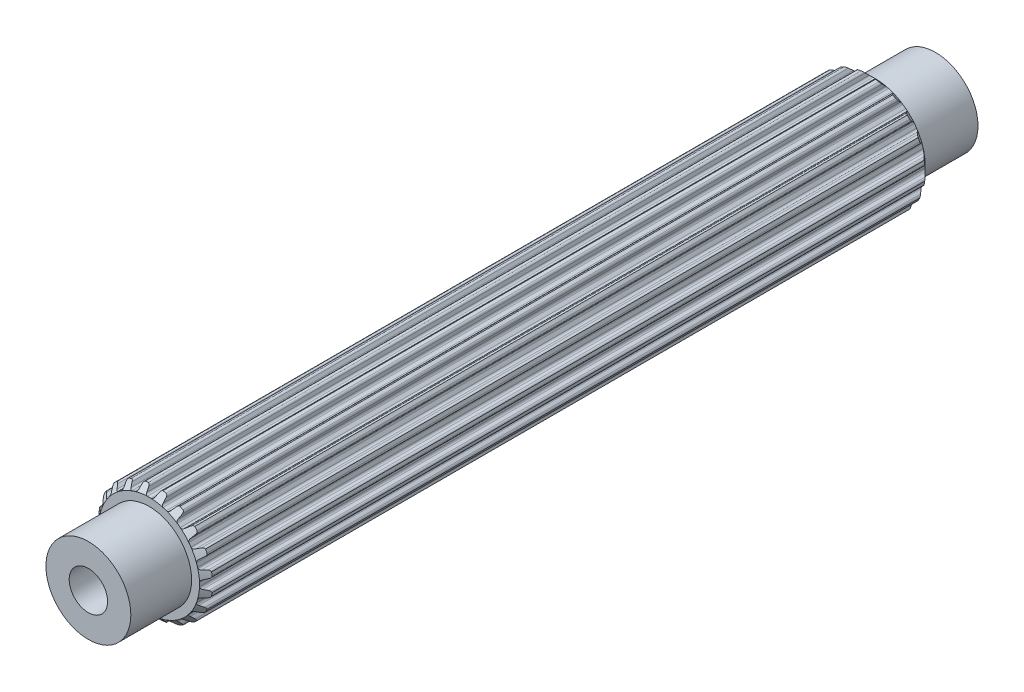
SolidWorks part; units mm, degrees
ref_plane "Front Plane" through (0, 0, 0) normal (0, 0, 1) x (1, 0, 0)
ref_plane "Top Plane" through (0, 0, 0) normal (0, 1, 0) x (1, 0, 0)
ref_plane "Right Plane" through (0, 0, 0) normal (1, 0, 0) x (0, 0, -1)
sketch "Sketch1" plane through (0, 0, 0) normal (0, 0, 1) x (1, 0, 0)
  line L0 (-0.1069, 2.9699) -> (0.1069, 2.9699)
  line L1 (0.3159, 3.2375) -> (0.2537, 3.0575)
  line L2 (-0.2964, 3.2367) -> (-0.2318, 3.0575)
  line L3 (-0.2964, 3.2367) -> (0.3159, 3.2375) construction
  line L4 (0, 3.3252) -> (0, 0) construction
  line L5 (-0.2318, 3.0575) -> (0.2537, 3.0575) construction
  line L6 (-0.4281, 3.3241) -> (0.4281, 3.3263) construction
  line L7 (0.7183, 3.1698) -> (0.7244, 2.9795)
  line L8 (0.816, 2.8576) -> (1.0195, 2.7915)
  line L9 (1.3009, 2.9815) -> (1.1862, 2.8295)
  line L10 (1.6627, 2.7927) -> (1.6097, 2.6099)
  line L11 (1.6591, 2.4655) -> (1.8322, 2.3398)
  line L12 (2.1585, 2.4335) -> (2.0025, 2.3245)
  line L13 (2.4443, 2.1423) -> (2.3374, 1.9847)
  line L14 (2.3398, 1.8322) -> (2.4655, 1.6591)
  line L15 (2.8049, 1.6474) -> (2.6228, 1.5919)
  line L16 (2.9866, 1.2821) -> (2.8363, 1.1653)
  line L17 (2.7915, 1.0195) -> (2.8576, 0.816)
  line L18 (3.1767, 0.7) -> (2.9863, 0.7035)
  line L19 (3.2367, 0.2964) -> (3.0575, 0.2318)
  line L20 (2.9699, 0.1069) -> (2.9699, -0.1069)
  line L21 (3.2375, -0.3159) -> (3.0575, -0.2537)
  line L22 (3.1698, -0.7183) -> (2.9795, -0.7244)
  line L23 (2.8576, -0.816) -> (2.7915, -1.0195)
  line L24 (2.9815, -1.3009) -> (2.8295, -1.1862)
  line L25 (2.7927, -1.6627) -> (2.6099, -1.6097)
  line L26 (2.4655, -1.6591) -> (2.3398, -1.8322)
  line L27 (2.4335, -2.1585) -> (2.3245, -2.0025)
  line L28 (2.1423, -2.4443) -> (1.9847, -2.3374)
  line L29 (1.8322, -2.3398) -> (1.6591, -2.4655)
  line L30 (1.6474, -2.8049) -> (1.5919, -2.6228)
  line L31 (1.2821, -2.9866) -> (1.1653, -2.8363)
  line L32 (1.0195, -2.7915) -> (0.816, -2.8576)
  line L33 (0.7, -3.1767) -> (0.7035, -2.9863)
  line L34 (0.2964, -3.2367) -> (0.2318, -3.0575)
  line L35 (0.1069, -2.9699) -> (-0.1069, -2.9699)
  line L36 (-0.3159, -3.2375) -> (-0.2537, -3.0575)
  line L37 (-0.7183, -3.1698) -> (-0.7244, -2.9795)
  line L38 (-0.816, -2.8576) -> (-1.0195, -2.7915)
  line L39 (-1.3009, -2.9815) -> (-1.1862, -2.8295)
  line L40 (-1.6627, -2.7927) -> (-1.6097, -2.6099)
  line L41 (-1.6591, -2.4655) -> (-1.8322, -2.3398)
  line L42 (-2.1585, -2.4335) -> (-2.0025, -2.3245)
  line L43 (-2.4443, -2.1423) -> (-2.3374, -1.9847)
  line L44 (-2.3398, -1.8322) -> (-2.4655, -1.6591)
  line L45 (-2.8049, -1.6474) -> (-2.6228, -1.5919)
  line L46 (-2.9866, -1.2821) -> (-2.8363, -1.1653)
  line L47 (-2.7915, -1.0195) -> (-2.8576, -0.816)
  line L48 (-3.1767, -0.7) -> (-2.9863, -0.7035)
  line L49 (-3.2367, -0.2964) -> (-3.0575, -0.2318)
  line L50 (-2.9699, -0.1069) -> (-2.9699, 0.1069)
  line L51 (-3.2375, 0.3159) -> (-3.0575, 0.2537)
  line L52 (-3.1698, 0.7183) -> (-2.9795, 0.7244)
  line L53 (-2.8576, 0.816) -> (-2.7915, 1.0195)
  line L54 (-2.9815, 1.3009) -> (-2.8295, 1.1862)
  line L55 (-2.7927, 1.6627) -> (-2.6099, 1.6097)
  line L56 (-2.4655, 1.6591) -> (-2.3398, 1.8322)
  line L57 (-2.4335, 2.1585) -> (-2.3245, 2.0025)
  line L58 (-2.1423, 2.4443) -> (-1.9847, 2.3374)
  line L59 (-1.8322, 2.3398) -> (-1.6591, 2.4655)
  line L60 (-1.6474, 2.8049) -> (-1.5919, 2.6228)
  line L61 (-1.2821, 2.9866) -> (-1.1653, 2.8363)
  line L62 (-1.0195, 2.7915) -> (-0.816, 2.8576)
  line L63 (-0.7, 3.1767) -> (-0.7035, 2.9863)
  line L64 (0.4281, 3.3263) -> (0.62, 3.2938)
  line L65 (1.4351, 3.0312) -> (1.6075, 2.9409)
  line L66 (2.3015, 2.4394) -> (2.4376, 2.3003)
  line L67 (2.9427, 1.6088) -> (3.0291, 1.4344)
  line L68 (3.2958, 0.6207) -> (3.3241, 0.4281)
  line L69 (3.3263, -0.4281) -> (3.2938, -0.62)
  line L70 (3.0312, -1.4351) -> (2.9409, -1.6075)
  line L71 (2.4394, -2.3015) -> (2.3003, -2.4376)
  line L72 (1.6088, -2.9427) -> (1.4344, -3.0291)
  line L73 (0.6207, -3.2958) -> (0.4281, -3.3241)
  line L74 (-0.4281, -3.3263) -> (-0.62, -3.2938)
  line L75 (-1.4351, -3.0312) -> (-1.6075, -2.9409)
  line L76 (-2.3015, -2.4394) -> (-2.4376, -2.3003)
  line L77 (-2.9427, -1.6088) -> (-3.0291, -1.4344)
  line L78 (-3.2958, -0.6207) -> (-3.3241, -0.4281)
  line L79 (-3.3263, 0.4281) -> (-3.2938, 0.62)
  line L80 (-3.0312, 1.4351) -> (-2.9409, 1.6075)
  line L81 (-2.4394, 2.3015) -> (-2.3003, 2.4376)
  line L82 (-1.6088, 2.9427) -> (-1.4344, 3.0291)
  line L83 (-0.6207, 3.2958) -> (-0.4281, 3.3241)
  arc A0 (0.2537, 3.0575) -> (0.1069, 2.9699) centre (0.1283, 3.1009) cw
  arc A1 (-0.2318, 3.0575) -> (-0.1069, 2.9699) centre (-0.1069, 3.1026) ccw
  arc A2 (0.62, 3.2938) -> (0.7183, 3.1698) centre (0.5856, 3.1656) cw
  arc A3 (0.7244, 2.9795) -> (0.816, 2.8576) centre (0.857, 2.9838) ccw
  arc A4 (-0.4281, 3.3241) -> (-0.2964, 3.2367) centre (-0.4213, 3.1916) cw
  arc A5 (0.4281, 3.3263) -> (0.3159, 3.2375) centre (0.4413, 3.1942) ccw
  arc A6 (1.1862, 2.8295) -> (1.0195, 2.7915) centre (1.0802, 2.9095) cw
  arc A7 (1.4351, 3.0312) -> (1.3009, 2.9815) centre (1.4068, 2.9015) ccw
  arc A8 (1.6075, 2.9409) -> (1.6627, 2.7927) centre (1.5352, 2.8297) cw
  arc A9 (1.6097, 2.6099) -> (1.6591, 2.4655) centre (1.7371, 2.5729) ccw
  arc A10 (2.0025, 2.3245) -> (1.8322, 2.3398) centre (1.9264, 2.4332) cw
  arc A11 (2.3015, 2.4394) -> (2.1585, 2.4335) centre (2.2346, 2.3248) ccw
  arc A12 (2.4376, 2.3003) -> (2.4443, 2.1423) centre (2.3345, 2.2168) cw
  arc A13 (2.3374, 1.9847) -> (2.3398, 1.8322) centre (2.4472, 1.9102) ccw
  arc A14 (2.6228, 1.5919) -> (2.4655, 1.6591) centre (2.5841, 1.7189) cw
  arc A15 (2.9427, 1.6088) -> (2.8049, 1.6474) centre (2.8436, 1.5205) ccw
  arc A16 (3.0291, 1.4344) -> (2.9866, 1.2821) centre (2.9052, 1.3869) cw
  arc A17 (2.8363, 1.1653) -> (2.7915, 1.0195) centre (2.9177, 1.0605) ccw
  arc A18 (2.9863, 0.7035) -> (2.8576, 0.816) centre (2.9887, 0.8362) cw
  arc A19 (3.2958, 0.6207) -> (3.1767, 0.7) centre (3.1743, 0.5673) ccw
  arc A20 (3.3241, 0.4281) -> (3.2367, 0.2964) centre (3.1916, 0.4213) cw
  arc A21 (3.0575, 0.2318) -> (2.9699, 0.1069) centre (3.1026, 0.1069) ccw
  arc A22 (3.0575, -0.2537) -> (2.9699, -0.1069) centre (3.1009, -0.1283) cw
  arc A23 (3.3263, -0.4281) -> (3.2375, -0.3159) centre (3.1942, -0.4413) ccw
  arc A24 (3.2938, -0.62) -> (3.1698, -0.7183) centre (3.1656, -0.5856) cw
  arc A25 (2.9795, -0.7244) -> (2.8576, -0.816) centre (2.9838, -0.857) ccw
  arc A26 (2.8295, -1.1862) -> (2.7915, -1.0195) centre (2.9095, -1.0802) cw
  arc A27 (3.0312, -1.4351) -> (2.9815, -1.3009) centre (2.9015, -1.4068) ccw
  arc A28 (2.9409, -1.6075) -> (2.7927, -1.6627) centre (2.8297, -1.5352) cw
  arc A29 (2.6099, -1.6097) -> (2.4655, -1.6591) centre (2.5729, -1.7371) ccw
  arc A30 (2.3245, -2.0025) -> (2.3398, -1.8322) centre (2.4332, -1.9264) cw
  arc A31 (2.4394, -2.3015) -> (2.4335, -2.1585) centre (2.3248, -2.2346) ccw
  arc A32 (2.3003, -2.4376) -> (2.1423, -2.4443) centre (2.2168, -2.3345) cw
  arc A33 (1.9847, -2.3374) -> (1.8322, -2.3398) centre (1.9102, -2.4472) ccw
  arc A34 (1.5919, -2.6228) -> (1.6591, -2.4655) centre (1.7189, -2.5841) cw
  arc A35 (1.6088, -2.9427) -> (1.6474, -2.8049) centre (1.5205, -2.8436) ccw
  arc A36 (1.4344, -3.0291) -> (1.2821, -2.9866) centre (1.3869, -2.9052) cw
  arc A37 (1.1653, -2.8363) -> (1.0195, -2.7915) centre (1.0605, -2.9177) ccw
  arc A38 (0.7035, -2.9863) -> (0.816, -2.8576) centre (0.8362, -2.9887) cw
  arc A39 (0.6207, -3.2958) -> (0.7, -3.1767) centre (0.5673, -3.1743) ccw
  arc A40 (0.4281, -3.3241) -> (0.2964, -3.2367) centre (0.4213, -3.1916) cw
  arc A41 (0.2318, -3.0575) -> (0.1069, -2.9699) centre (0.1069, -3.1026) ccw
  arc A42 (-0.2537, -3.0575) -> (-0.1069, -2.9699) centre (-0.1283, -3.1009) cw
  arc A43 (-0.4281, -3.3263) -> (-0.3159, -3.2375) centre (-0.4413, -3.1942) ccw
  arc A44 (-0.62, -3.2938) -> (-0.7183, -3.1698) centre (-0.5856, -3.1656) cw
  arc A45 (-0.7244, -2.9795) -> (-0.816, -2.8576) centre (-0.857, -2.9838) ccw
  arc A46 (-1.1862, -2.8295) -> (-1.0195, -2.7915) centre (-1.0802, -2.9095) cw
  arc A47 (-1.4351, -3.0312) -> (-1.3009, -2.9815) centre (-1.4068, -2.9015) ccw
  arc A48 (-1.6075, -2.9409) -> (-1.6627, -2.7927) centre (-1.5352, -2.8297) cw
  arc A49 (-1.6097, -2.6099) -> (-1.6591, -2.4655) centre (-1.7371, -2.5729) ccw
  arc A50 (-2.0025, -2.3245) -> (-1.8322, -2.3398) centre (-1.9264, -2.4332) cw
  arc A51 (-2.3015, -2.4394) -> (-2.1585, -2.4335) centre (-2.2346, -2.3248) ccw
  arc A52 (-2.4376, -2.3003) -> (-2.4443, -2.1423) centre (-2.3345, -2.2168) cw
  arc A53 (-2.3374, -1.9847) -> (-2.3398, -1.8322) centre (-2.4472, -1.9102) ccw
  arc A54 (-2.6228, -1.5919) -> (-2.4655, -1.6591) centre (-2.5841, -1.7189) cw
  arc A55 (-2.9427, -1.6088) -> (-2.8049, -1.6474) centre (-2.8436, -1.5205) ccw
  arc A56 (-3.0291, -1.4344) -> (-2.9866, -1.2821) centre (-2.9052, -1.3869) cw
  arc A57 (-2.8363, -1.1653) -> (-2.7915, -1.0195) centre (-2.9177, -1.0605) ccw
  arc A58 (-2.9863, -0.7035) -> (-2.8576, -0.816) centre (-2.9887, -0.8362) cw
  arc A59 (-3.2958, -0.6207) -> (-3.1767, -0.7) centre (-3.1743, -0.5673) ccw
  arc A60 (-3.3241, -0.4281) -> (-3.2367, -0.2964) centre (-3.1916, -0.4213) cw
  arc A61 (-3.0575, -0.2318) -> (-2.9699, -0.1069) centre (-3.1026, -0.1069) ccw
  arc A62 (-3.0575, 0.2537) -> (-2.9699, 0.1069) centre (-3.1009, 0.1283) cw
  arc A63 (-3.3263, 0.4281) -> (-3.2375, 0.3159) centre (-3.1942, 0.4413) ccw
  arc A64 (-3.2938, 0.62) -> (-3.1698, 0.7183) centre (-3.1656, 0.5856) cw
  arc A65 (-2.9795, 0.7244) -> (-2.8576, 0.816) centre (-2.9838, 0.857) ccw
  arc A66 (-2.8295, 1.1862) -> (-2.7915, 1.0195) centre (-2.9095, 1.0802) cw
  arc A67 (-3.0312, 1.4351) -> (-2.9815, 1.3009) centre (-2.9015, 1.4068) ccw
  arc A68 (-2.9409, 1.6075) -> (-2.7927, 1.6627) centre (-2.8297, 1.5352) cw
  arc A69 (-2.6099, 1.6097) -> (-2.4655, 1.6591) centre (-2.5729, 1.7371) ccw
  arc A70 (-2.3245, 2.0025) -> (-2.3398, 1.8322) centre (-2.4332, 1.9264) cw
  arc A71 (-2.4394, 2.3015) -> (-2.4335, 2.1585) centre (-2.3248, 2.2346) ccw
  arc A72 (-2.3003, 2.4376) -> (-2.1423, 2.4443) centre (-2.2168, 2.3345) cw
  arc A73 (-1.9847, 2.3374) -> (-1.8322, 2.3398) centre (-1.9102, 2.4472) ccw
  arc A74 (-1.5919, 2.6228) -> (-1.6591, 2.4655) centre (-1.7189, 2.5841) cw
  arc A75 (-1.6088, 2.9427) -> (-1.6474, 2.8049) centre (-1.5205, 2.8436) ccw
  arc A76 (-1.4344, 3.0291) -> (-1.2821, 2.9866) centre (-1.3869, 2.9052) cw
  arc A77 (-1.1653, 2.8363) -> (-1.0195, 2.7915) centre (-1.0605, 2.9177) ccw
  arc A78 (-0.7035, 2.9863) -> (-0.816, 2.8576) centre (-0.8362, 2.9887) cw
  arc A79 (-0.6207, 3.2958) -> (-0.7, 3.1767) centre (-0.5673, 3.1743) ccw
  point P14 (0, 2.9699)
  point P247 (0, 0)
  dimension "D4" = 0.1327
  dimension "D8" = 20
  dimension "D1" = 2.9699
  dimension "D2" = 0.2139
  dimension "D3" = 0.1904
  dimension "D5" = 0.0877
  dimension "D6" = 0.4855
  dimension "D7" = 0.8563
extrude "Boss-Extrude1" add sketch "Sketch1" along normal mid plane 42.7584
sketch "Sketch2" plane through (0, 0, 0) normal (0, 0, 1) x (1, 0, 0)
  circle A0 centre (0, 0) radius 2.5019
  dimension "D1" = 5.0038
extrude "Boss-Extrude2" add sketch "Sketch2" along normal mid plane 49.9212
sketch "Sketch4" plane through (0, 0, 24.9606) normal (0, 0, 1) x (1, 0, 0)
  circle A0 centre (0, 0) radius 2.5019 construction
  point P0 (0, 0)
sketch "Sketch5" plane through (0, 0, -24.9606) normal (0, 0, -1) x (-1, 0, 0)
  circle A0 centre (0, 0) radius 2.5019 construction
  point P0 (0, 0)
sketch "Sketch3" plane through (0, 0, 0) normal (1, 0, 0) x (0, 0, -1)
  line L0 (-20.248, 4.1011) -> (-21.3792, 2.9699)
  line L1 (-21.3792, 2.9699) -> (-21.3792, 4.1011)
  line L2 (-21.3792, 4.1011) -> (-20.248, 4.1011)
  line L3 (-21.3792, 2.5019) -> (-21.3792, -2.5019) construction
  line L5 (-14.3608, 0) -> (13.2171, 0) construction
  line L7 (21.3792, 18.093) -> (21.3792, 2.9699)
  line L8 (21.3792, 2.9699) -> (13.8176, 10.5315)
  line L9 (13.8176, 10.5315) -> (21.3792, 18.093)
  line L10 (21.3792, -2.5019) -> (21.3792, 2.5019) construction
  point P6 (-4.866, 6.1438)
  dimension "D1" = 45
  dimension "D2" = 45
revolve "Cut-Revolve1" cut sketch "Sketch3" angle 360 about L5
sketch "Sketch6" plane through (0, 0, 0) normal (0, 0, 1) x (1, 0, 0)
  circle A0 centre (0, 0) radius 1.1303
  dimension "D1" = 2.2606
extrude "Cut-Extrude1" cut sketch "Sketch6" against normal up to surface and the other way up to surface up to face at (2.5019, 0, -24.9606) other way up to face at (2.5019, 0, 24.9606)
sketch "Sketch7" plane through (0, 0, 0) normal (0, 0, 1) x (1, 0, 0)
  circle A0 centre (0, 0) radius 1.1303
  circle A1 centre (0, 0) radius 1.1303 construction
extrude "Boss-Extrude3" add sketch "Sketch7" against normal offset from surface 9.525 and the other way offset from surface (15.4356 mm away) 9.525 up to face at (1.1303, 0, -24.9606) other way up to face at (1.1303, 0, 24.9606)
